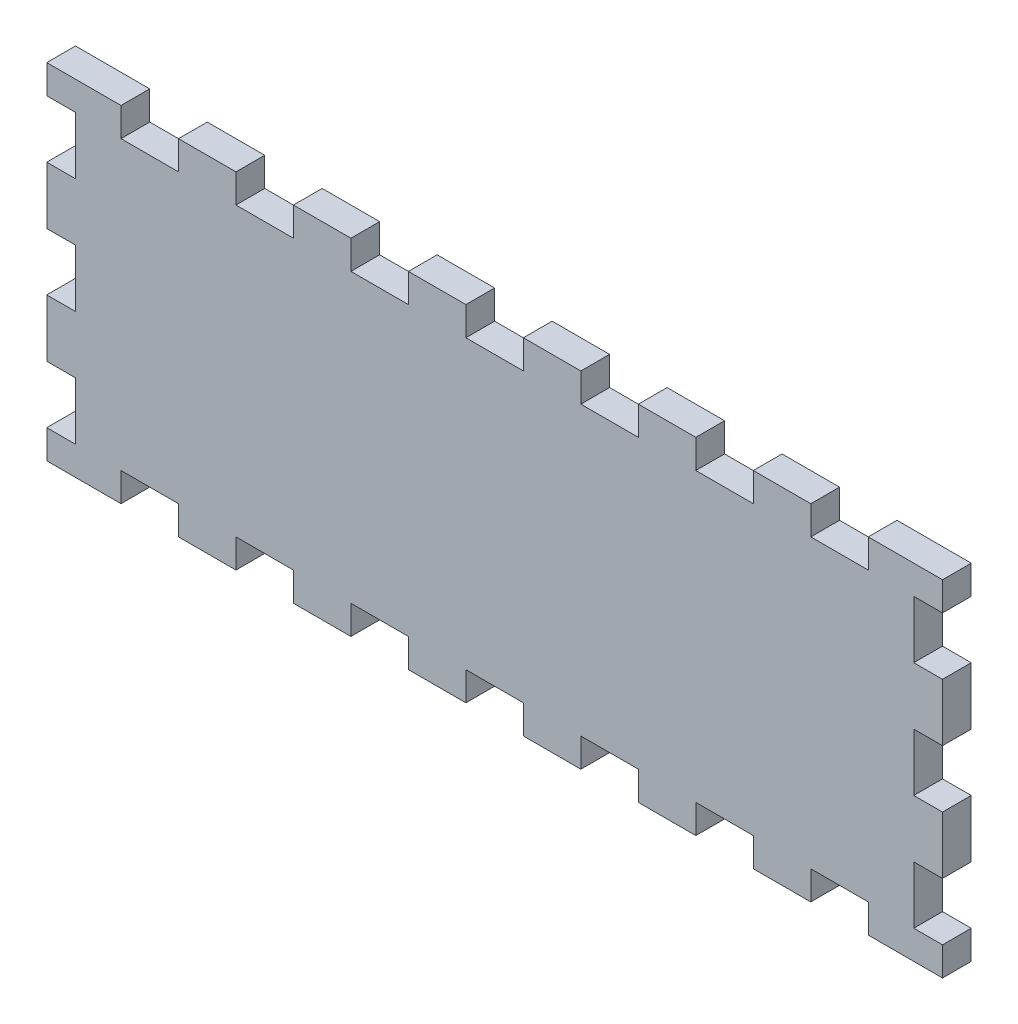
SolidWorks part; units mm, degrees
ref_plane "Front Plane" through (0, 0, 0) normal (0, 0, 1) x (1, 0, 0)
ref_plane "Top Plane" through (0, 0, 0) normal (0, 1, 0) x (1, 0, 0)
ref_plane "Right Plane" through (0, 0, 0) normal (1, 0, 0) x (0, 0, -1)
sketch "Sketch1" plane through (0, 0, 0) normal (0, 0, 1) x (1, 0, 0)
  line L1 (-93.5, 6) -> (-93.5, -66)
  line L2 (93.5, 6) -> (93.5, -66)
  line L3 (-93.5, -66) -> (93.5, -66)
  line L4 (-78, 6) -> (-78, 0)
  line L5 (-78, 0) -> (-66, 0)
  line L6 (-66, 0) -> (-66, 6)
  line L7 (-54, 6) -> (-54, 0)
  line L8 (-54, 0) -> (-42, 0)
  line L9 (-42, 0) -> (-42, 6)
  line L10 (-30, 6) -> (-30, 0)
  line L11 (-30, 0) -> (-18, 0)
  line L12 (-18, 0) -> (-18, 6)
  line L13 (-18, 6) -> (-6, 6)
  line L14 (-6, 6) -> (-6, 0)
  line L15 (-6, 0) -> (6, 0)
  line L16 (6, 0) -> (6, 6)
  line L17 (6, 6) -> (18, 6)
  line L18 (18, 6) -> (18, 0)
  line L19 (18, 0) -> (30, 0)
  line L20 (30, 0) -> (30, 6)
  line L21 (30, 6) -> (42, 6)
  line L22 (42, 6) -> (42, 0)
  line L23 (42, 0) -> (54, 0)
  line L24 (54, 0) -> (54, 6)
  line L25 (54, 6) -> (66, 6)
  line L26 (66, 6) -> (66, 0)
  line L27 (66, 0) -> (78, 0)
  line L28 (78, 0) -> (78, 6)
  line L29 (78, 6) -> (93.5, 6)
  line L30 (-30, 6) -> (-42, 6)
  line L31 (-54, 6) -> (-66, 6)
  line L32 (-78, 6) -> (-93.5, 6)
  line L33 (-93.5, -66) -> (93.5, -66)
  line L34 (93.5, 0) -> (93.5, -12)
  line L35 (93.5, 0) -> (87.5, 0)
  line L36 (93.5, -12) -> (87.5, -12)
  line L37 (87.5, 0) -> (87.5, -12)
  line L38 (-87.5, 0) -> (-87.5, -12)
  line L39 (-87.5, 0) -> (-93.5, 0)
  line L40 (-93.5, 0) -> (-93.5, -12)
  line L41 (-87.5, -12) -> (-93.5, -12)
  line L42 (-87.5, -24) -> (-87.5, -36)
  line L43 (-87.5, -24) -> (-93.5, -24)
  line L44 (-93.5, -24) -> (-93.5, -36)
  line L45 (-87.5, -36) -> (-93.5, -36)
  line L46 (-87.5, -48) -> (-87.5, -60)
  line L47 (-87.5, -48) -> (-93.5, -48)
  line L48 (-93.5, -48) -> (-93.5, -60)
  line L49 (-87.5, -60) -> (-93.5, -60)
  line L50 (93.5, -24) -> (93.5, -36)
  line L51 (93.5, -24) -> (87.5, -24)
  line L52 (87.5, -24) -> (87.5, -36)
  line L53 (93.5, -36) -> (87.5, -36)
  line L54 (93.5, -48) -> (93.5, -60)
  line L55 (93.5, -48) -> (87.5, -48)
  line L56 (87.5, -48) -> (87.5, -60)
  line L57 (93.5, -60) -> (87.5, -60)
  line L58 (93.5, 0) -> (-87.5, 0) construction
  dimension "D1" = 6
  dimension "D2" = 12
  dimension "D3" = 2
  dimension "D4" = 3
  dimension "D5" = 181
  dimension "D6" = 6
  dimension "D7" = 12
extrude "Boss-Extrude3" add sketch "Sketch1" along normal blind 6 from offset 0 contours L34 L35 L37 L36 | L32 L1 L3 L2 L29 L28 L27 L26 L25 L24 L23 L22 L21 L20 L19 L18 L17 L16 L15 L14 L13 L12 L11 L10 L30 L9 L8 L7 L31 L6 L5 L4 | L50 L53 L52 L51 | L54 L57 L56 L55
sketch "Sketch3" plane through (0, 0, 6) normal (0, 0, 1) x (1, 0, 0)
  line L0 (-93.5, 0) -> (-93.5, -12)
  line L1 (-93.5, 0) -> (-87.5, 0)
  line L2 (-93.5, -12) -> (-87.5, -12)
  line L3 (-87.5, 0) -> (-87.5, -12)
  line L4 (-93.5, 6) -> (-93.5, -66) construction
  line L5 (-78, 6) -> (-93.5, 6) construction
  line L6 (87.5, 0) -> (87.5, -12)
  line L7 (87.5, 0) -> (93.5, 0)
  line L8 (93.5, 0) -> (93.5, -12)
  line L9 (87.5, -12) -> (93.5, -12)
  line L10 (87.5, -24) -> (87.5, -36)
  line L11 (87.5, -24) -> (93.5, -24)
  line L12 (93.5, -24) -> (93.5, -36)
  line L13 (87.5, -36) -> (93.5, -36)
  line L14 (87.5, -48) -> (87.5, -60)
  line L15 (87.5, -48) -> (93.5, -48)
  line L16 (93.5, -48) -> (93.5, -60)
  line L17 (87.5, -60) -> (93.5, -60)
  line L18 (-93.5, -24) -> (-93.5, -36)
  line L19 (-93.5, -24) -> (-87.5, -24)
  line L20 (-87.5, -24) -> (-87.5, -36)
  line L21 (-93.5, -36) -> (-87.5, -36)
  line L22 (-93.5, -48) -> (-93.5, -60)
  line L23 (-93.5, -48) -> (-87.5, -48)
  line L24 (-87.5, -48) -> (-87.5, -60)
  line L25 (-93.5, -60) -> (-87.5, -60)
  line L26 (-93.5, 0) -> (87.5, 0) construction
  dimension "D1" = 6
  dimension "D2" = 6
  dimension "D3" = 12
  dimension "D6" = 181
  dimension "D4" = 2
  dimension "D5" = 3
extrude "Cut-Extrude1" cut sketch "Sketch3" against normal blind 6
sketch "Sketch4" plane through (0, 0, 6) normal (0, 0, 1) x (1, 0, 0)
  line L0 (-78, -66) -> (-66, -66)
  line L1 (-78, -66) -> (-78, -60)
  line L2 (-66, -66) -> (-66, -60)
  line L3 (-78, -60) -> (-66, -60)
  line L4 (-93.5, -66) -> (93.5, -66) construction
  line L8 (-93.5, -60) -> (-93.5, -66) construction
  line L9 (-54, -66) -> (-42, -66)
  line L10 (-54, -66) -> (-54, -60)
  line L11 (-54, -60) -> (-42, -60)
  line L12 (-42, -66) -> (-42, -60)
  line L13 (-30, -66) -> (-18, -66)
  line L14 (-30, -66) -> (-30, -60)
  line L15 (-30, -60) -> (-18, -60)
  line L16 (-18, -66) -> (-18, -60)
  line L17 (-6, -66) -> (6, -66)
  line L18 (-6, -66) -> (-6, -60)
  line L19 (-6, -60) -> (6, -60)
  line L20 (6, -66) -> (6, -60)
  line L21 (18, -66) -> (30, -66)
  line L22 (18, -66) -> (18, -60)
  line L23 (18, -60) -> (30, -60)
  line L24 (30, -66) -> (30, -60)
  line L25 (42, -66) -> (54, -66)
  line L26 (42, -66) -> (42, -60)
  line L27 (42, -60) -> (54, -60)
  line L28 (54, -66) -> (54, -60)
  line L29 (66, -66) -> (78, -66)
  line L30 (66, -66) -> (66, -60)
  line L31 (66, -60) -> (78, -60)
  line L32 (78, -66) -> (78, -60)
  line L33 (-78, -66) -> (-54, -66) construction
  dimension "D1" = 12
  dimension "D2" = 6
  dimension "D3" = 15.5
  dimension "D5" = 24
  dimension "D4" = 7
extrude "Cut-Extrude2" cut sketch "Sketch4" against normal blind 6
